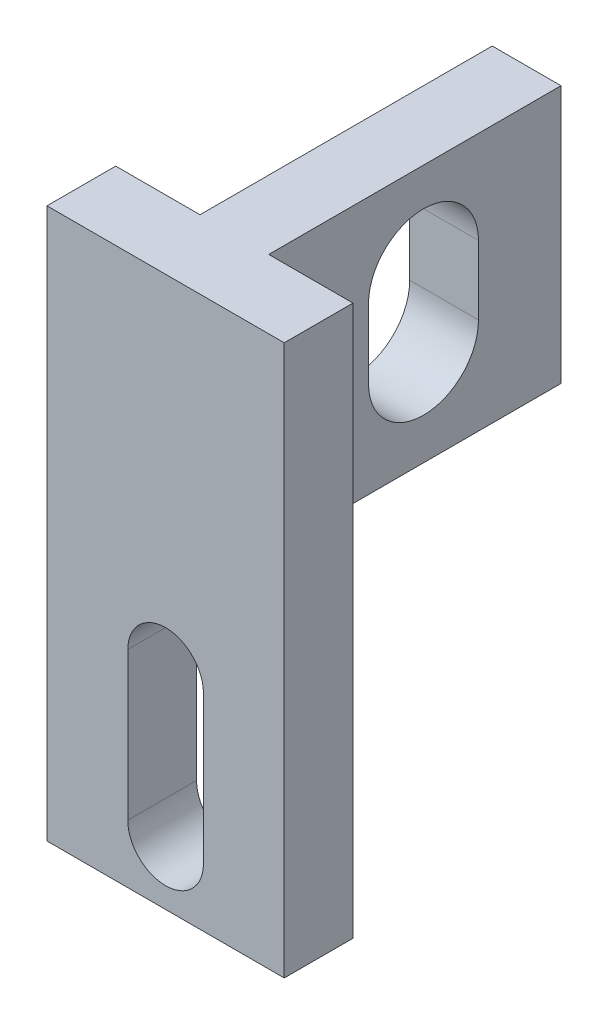
SolidWorks part; units mm, degrees
material "6061-T6 (SS)"
ref_plane "Front Plane" through (0, 0, 0) normal (0, 0, 1) x (1, 0, 0)
ref_plane "Top Plane" through (0, 0, 0) normal (0, 1, 0) x (1, 0, 0)
ref_plane "Right Plane" through (0, 0, 0) normal (1, 0, 0) x (0, 0, -1)
sketch "Sketch7" plane through (0, 0, 0) normal (0, 0, 1) x (1, 0, 0)
  line L1 (-11.4569, 21.3402) -> (-18.4569, 21.3402)
  line L2 (-11.4569, 21.3402) -> (-11.4569, 5.3402)
  line L3 (-11.4569, 5.3402) -> (-18.4569, 5.3402)
  line L4 (-18.4569, 21.3402) -> (-18.4569, 5.3402)
  dimension "D1" = 7
  dimension "D2" = 16
extrude "Boss-Extrude6" add sketch "Sketch7" along normal blind 2
sketch "Sketch8" plane through (0, 0, 0) normal (0, 0, -1) x (-1, 0, 0)
  line L0 (11.4569, 21.3402) -> (18.4569, 21.3402) construction
  line L1 (13.9569, 21.3402) -> (15.9569, 21.3402)
  line L2 (13.9569, 21.3402) -> (13.9569, 13.8402)
  line L3 (13.9569, 13.8402) -> (15.9569, 13.8402)
  line L4 (15.9569, 21.3402) -> (15.9569, 13.8402)
  line L6 (11.4569, 5.3402) -> (11.4569, 21.3402) construction
  dimension "D1" = 7.5
  dimension "D3" = 2
  dimension "D4" = 2.5
extrude "Boss-Extrude7" add sketch "Sketch8" along normal blind 8.5
hole_wizard "Ø2.2 (2.2) Diameter Hole1" positions "Sketch13" profile "Sketch12" hole size "Ø2.2" standard "ANSI Metric"
sketch "Sketch13" plane through (0, 0, 0) normal (0, 0, -1) x (-1, 0, 0)
  line L2 (13.9569, 13.8402) -> (15.9569, 13.8402) construction
  line L3 (11.4569, 5.3402) -> (11.4569, 21.3402) construction
  point P0 (14.9569, 11.3402)
  dimension "D1" = 2.5
  dimension "D2" = 3.5
sketch "Sketch12" plane through (-14.9569, 11.3402, 0) normal (1, 0, 0) x (0, 1, 0)
  line L0 (0, 0) -> (0, 2)
  line L1 (0, 2) -> (1.1, 2)
  line L2 (1.1, 2) -> (1.1, 0)
  line L5 (1.1, 0) -> (0, 0)
  line L10 (0, 2) -> (-1.1, 2) construction
  line L11 (0, -6.35) -> (0, 107.95) construction
  dimension "Hole Dia." = 2.2
  dimension "Hole Depth" = 2
  dimension "Drill Angle" = 180
sketch "Sketch15" plane through (-13.9569, 0, 0) normal (1, 0, 0) x (0, 0, -1)
  line L0 (2.9, 16.6402) -> (2.9, 18.6402)
  line L1 (6.1, 16.6402) -> (6.1, 18.6402)
  line L2 (8.5, 21.3402) -> (8.5, 13.8402) construction
  line L3 (8.5, 21.3402) -> (0, 21.3402) construction
  arc A1 (6.1, 18.6402) -> (2.9, 18.6402) centre (4.5, 18.6402) ccw
  arc A3 (2.9, 16.6402) -> (6.1, 16.6402) centre (4.5, 16.6402) ccw
  dimension "D1" = 4
  dimension "D2" = 2
  dimension "D3" = 2
  dimension "D5" = 1.6
  dimension "D6" = 1.6
  dimension "D4" = 2.7
extrude "Cut-Extrude3" cut sketch "Sketch15" against normal through all
sketch "Sketch17" plane through (0, 0, 0) normal (0, 0, -1) x (-1, 0, 0)
  line L0 (13.8569, 7.0402) -> (13.8569, 11.3402)
  line L1 (16.0569, 7.0402) -> (16.0569, 11.3402)
  line L2 (16.0569, 11.3402) -> (13.8569, 11.3402)
  arc A2 (13.8569, 7.0402) -> (16.0569, 7.0402) centre (14.9569, 7.0402) ccw
  circle A3 centre (14.9569, 11.3402) radius 1.1 construction
  dimension "D2" = 4.3
extrude "Cut-Extrude5" cut sketch "Sketch17" against normal blind 10
sketch "Sketch18" plane through (0, 0, 0) normal (0, 0, -1) x (-1, 0, 0)
  line L0 (18.4569, 5.3402) -> (11.4569, 5.3402) construction
  line L1 (11.4569, 21.3402) -> (11.5069, 21.3402)
  line L2 (11.4569, 21.3402) -> (11.4569, 5.3402)
  line L3 (11.4569, 5.3402) -> (11.5069, 5.3402)
  line L4 (11.5069, 21.3402) -> (11.5069, 5.3402)
  line L6 (18.4569, 21.3402) -> (18.4069, 21.3402)
  line L7 (18.4569, 21.3402) -> (18.4569, 5.3402)
  line L8 (18.4569, 5.3402) -> (18.4069, 5.3402)
  line L9 (18.4069, 21.3402) -> (18.4069, 5.3402)
  dimension "D1" = 0.05
  dimension "D2" = 0.05
extrude "Cut-Extrude6" cut sketch "Sketch18" against normal through all
